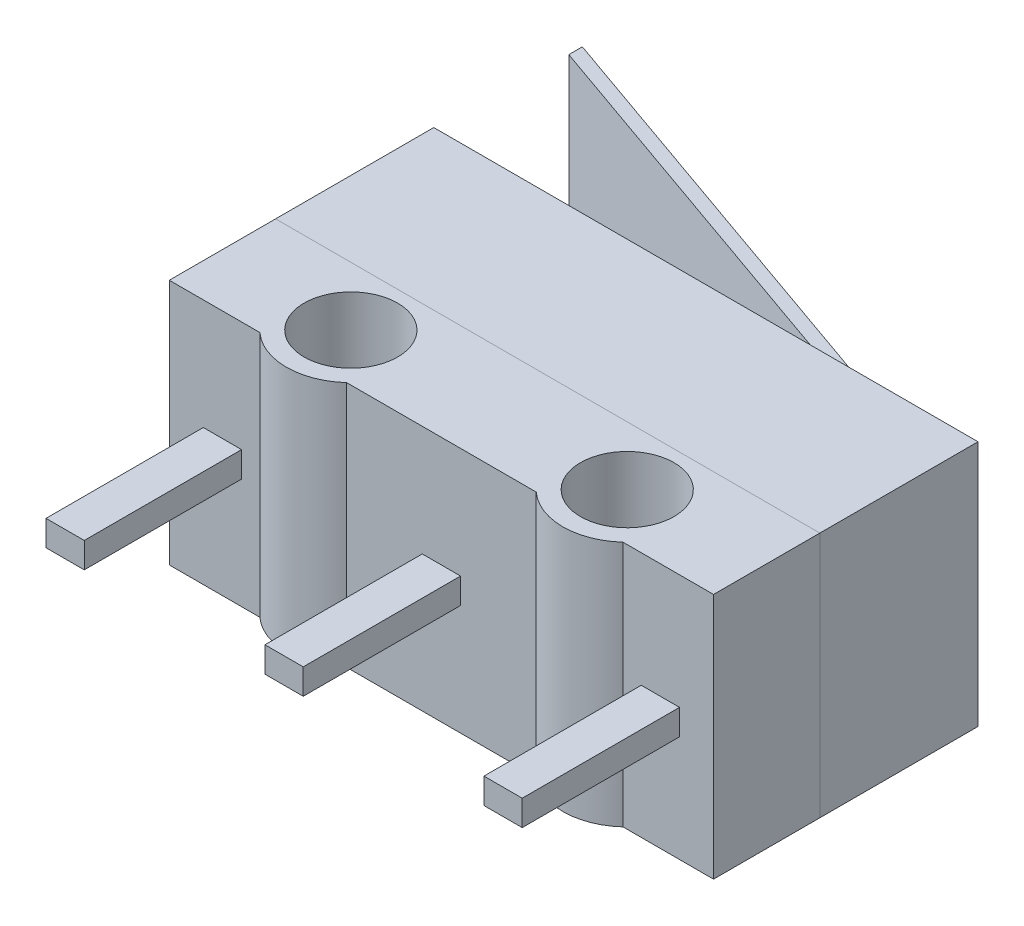
SolidWorks part; units mm, degrees
ref_plane "Front Plane" through (0, 0, 0) normal (0, 0, 1) x (1, 0, 0)
ref_plane "Top Plane" through (0, 0, 0) normal (0, 1, 0) x (1, 0, 0)
ref_plane "Right Plane" through (0, 0, 0) normal (1, 0, 0) x (0, 0, -1)
sketch "Sketch2" plane through (0, 0, 0) normal (0, 0, 1) x (1, 0, 0)
  line L1 (0, 0) -> (-12.8, 0)
  line L2 (0, 0) -> (0, 5.8)
  line L3 (0, 5.8) -> (-12.8, 5.8)
  line L4 (-12.8, 0) -> (-12.8, 5.8)
  dimension "D1" = 12.8
  dimension "D2" = 5.8
extrude "Boss-Extrude1" add sketch "Sketch2" along normal blind 6.22 contours L3 L4 L1 L2
ref_plane "Plane1" through (0, 0, 6.57) normal (0, 0, 1) x (1, 0, 0)
hole_wizard "M2 Clearance Hole1" positions "Sketch14" profile "Sketch15" hole size "M2" standard "ANSI Metric" end condition through all
sketch "Sketch14" plane through (0, 0, 0) normal (0, -1, 0) x (-1, 0, 0)
  line L0 (0, -5.1) -> (12.8, -5.1) construction
  line L1 (0, -6.22) -> (0, 0) construction
  line L2 (12.8, -6.22) -> (12.8, 0) construction
  line L5 (0, 0) -> (12.8, 0) construction
  point P12 (3.15, -5.1)
  point P14 (9.65, -5.1)
  point P17 (6.4, -5.1)
  dimension "D2" = 6.5
  dimension "D3" = 3.25
  dimension "D1" = 5.1
sketch "Sketch15" plane through (-9.65, 0, 5.1) normal (1, 0, 0) x (0, 0, -1)
  line L0 (0, 0) -> (0, 5.8)
  line L1 (0, 5.8) -> (1.1, 5.8)
  line L2 (1.1, 5.8) -> (1.1, 0)
  line L5 (1.1, 0) -> (0, 0)
  line L11 (0, -6.35) -> (0, 107.95) construction
  dimension "Thru Hole Dia." = 2.2
  dimension "Thru Hole Depth" = 5.8
sketch "Sketch16" plane through (0, 0, 0) normal (0, -1, 0) x (1, 0, 0)
  line L1 (-10.6702, 6.22) -> (-8.6298, 6.22)
  line L3 (-4.1702, 6.22) -> (-2.1298, 6.22)
  line L4 (0, 6.22) -> (-12.8, 6.22) construction
  arc A0 (-2.1298, 6.22) -> (-4.1702, 6.22) centre (-3.15, 5.1) ccw
  arc A1 (-8.6298, 6.22) -> (-10.6702, 6.22) centre (-9.65, 5.1) ccw
  dimension "D1" = 3.03
  dimension "D2" = 3.03
extrude "Boss-Extrude2" add sketch "Sketch16" against normal through all
sketch "Sketch17" plane through (0, 0, 6.22) normal (0, 0, 1) x (1, 0, 0)
  line L0 (-12.8, 2.9) -> (0, 2.9) construction
  line L1 (-6.85, 3.2) -> (-5.95, 3.2)
  line L2 (-6.85, 3.2) -> (-6.85, 2.6)
  line L3 (-6.85, 2.6) -> (-5.95, 2.6)
  line L4 (-5.95, 3.2) -> (-5.95, 2.6)
  line L5 (-12.8, 0) -> (-12.8, 5.8) construction
  line L6 (0, 0) -> (0, 5.8) construction
  line L7 (-6.85, 3.2) -> (-5.95, 2.6) construction
  line L8 (-6.85, 2.6) -> (-5.95, 3.2) construction
  line L9 (-11.55, 3.2) -> (-11.55, 2.6) construction
  line L10 (-12, 3.2) -> (-11.1, 3.2)
  line L11 (-12, 3.2) -> (-12, 2.6)
  line L12 (-12, 2.6) -> (-11.1, 2.6)
  line L13 (-11.1, 3.2) -> (-11.1, 2.6)
  line L14 (-1.25, 3.1) -> (-1.25, 2.5) construction
  line L15 (-1.7, 3.1) -> (-0.8, 3.1)
  line L16 (-1.7, 3.1) -> (-1.7, 2.5)
  line L17 (-1.7, 2.5) -> (-0.8, 2.5)
  line L18 (-0.8, 3.1) -> (-0.8, 2.5)
  point P10 (-6.4, 2.9)
  point P11 (-6.4, 2.9)
  point P18 (-11.55, 2.9)
  dimension "D1" = 0.6
  dimension "D2" = 0.9
  dimension "D3" = 0.9
  dimension "D4" = 0.6
  dimension "D5" = 5.15
  dimension "D6" = 0.9
  dimension "D7" = 0.6
  dimension "D8" = 5.15
  dimension "D9" = 0.2
extrude "Boss-Extrude3" add sketch "Sketch17" along normal blind 3.7
ref_plane "Plane2" through (0, 1.35, 0) normal (0, 1, 0) x (1, 0, 0)
sketch "Sketch19" plane through (0, 1.35, 0) normal (0, 1, 0) x (1, 0, 0)
  line L0 (-1, 0) -> (-12.5401, 4.053) construction
  line L1 (0, 0) -> (-12.8, 0) construction
  line L2 (-12.8, 3.9853) -> (-12.8, 0) construction
  line L3 (-12.8, 0) -> (-1, 0)
  line L4 (-0.9503, 0.1415) -> (-14.0473, 4.7413)
  line L5 (-1.4527, 0) -> (-14.0473, 4.4233)
  line L6 (-0.9503, 0.1415) -> (-0.5473, 0)
  line L7 (-0.5473, 0) -> (-1.4527, 0)
  line L8 (-1.0497, -0.1415) -> (-12.5898, 3.9114) construction
  line L10 (-0.9503, 0.1415) -> (-12.4904, 4.1945) construction
  line L11 (-14.0473, 4.4233) -> (-14.0473, 4.7413)
  line L12 (-4.3, 1) -> (-4.3, 0)
  line L13 (0, -6.22) -> (0, 0) construction
  dimension "D1" = 1
  dimension "D2" = 4.3
  dimension "D5" = 13.5
  dimension "D6" = 1
  dimension "D3" = 0.15
  dimension "D4" = 0.15
extrude "Boss-Extrude5" add sketch "Sketch19" along normal blind 3.1
ref_plane "Plane3" through (0, 0, 3.72) normal (0, 0, 1) x (1, 0, 0)
split line "Split Line1"
equation "\"D3@Sketch14\"=\"D2@Sketch14\"/2"
equation "\"D1@Sketch16\"=2.2+1.5-0.35-0.32"
equation "\"D2@Sketch16\"=\"D1@Sketch16\""
equation "\"D3@Sketch17\"=\"D2@Sketch17\""
equation "\"D4@Sketch17\"=\"D1@Sketch17\""
equation "\"D6@Sketch17\"=\"D3@Sketch17\""
equation "\"D7@Sketch17\"=\"D1@Sketch17\""
